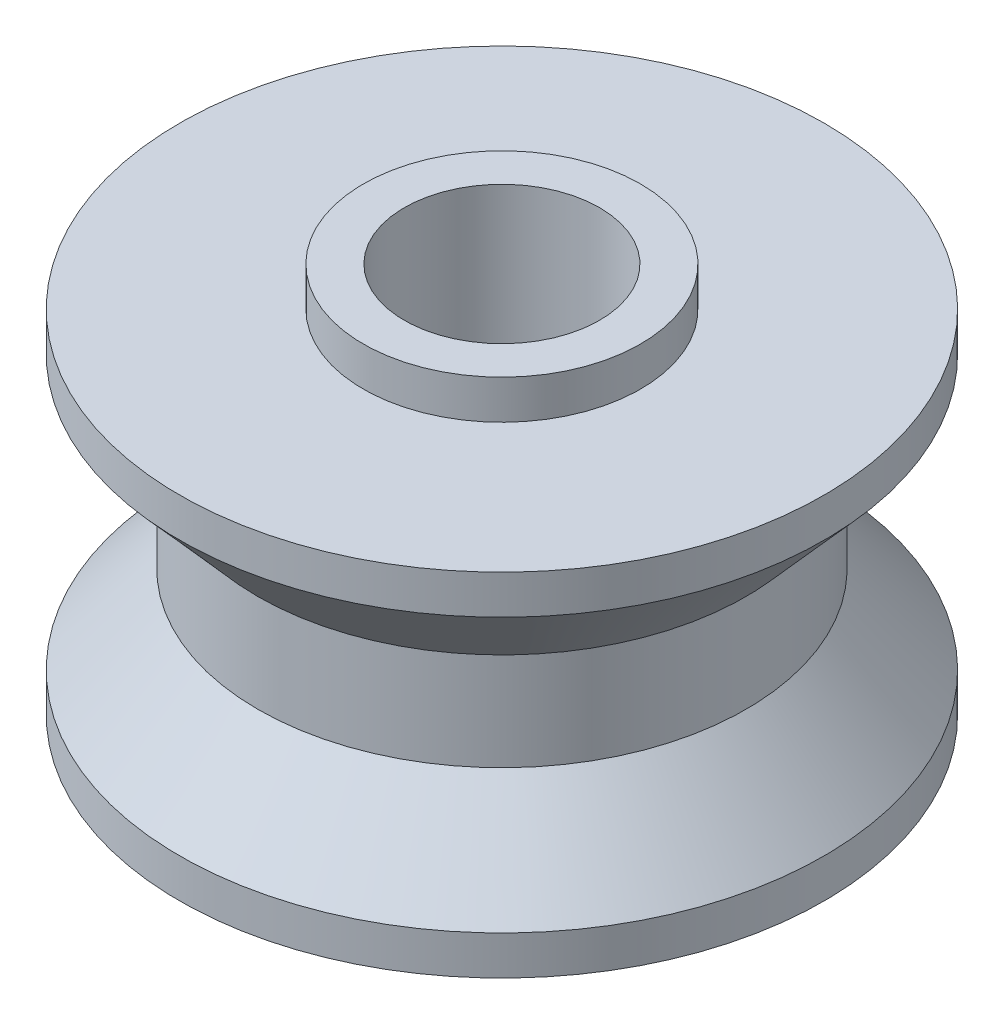
SolidWorks part; units mm, degrees
material "不锈钢 (铁素体)"
ref_plane "前视基准面" through (0, 0, 0) normal (0, 0, 1) x (1, 0, 0)
ref_plane "上视基准面" through (0, 0, 0) normal (0, 1, 0) x (1, 0, 0)
ref_plane "右视基准面" through (0, 0, 0) normal (1, 0, 0) x (0, 0, -1)
sketch "草图1" plane through (0, 0, 0) normal (0, 0, 1) x (1, 0, 0)
  line L0 (2.5, 5.5) -> (3.55, 5.5)
  line L1 (3.55, 5.5) -> (3.55, 4.5)
  line L2 (3.55, 4.5) -> (8.25, 4.5)
  line L3 (8.25, 4.5) -> (8.25, 3.5)
  line L4 (8.25, 3.5) -> (6.25, 1.25)
  line L5 (6.25, 1.25) -> (6.25, -1.25)
  line L6 (0, 0) -> (6.25, 0) construction
  line L7 (2.5, 5.5) -> (2.5, -5.5)
  line L8 (0, 0) -> (0, 4.5455) construction
  line L9 (8.25, -3.5) -> (6.25, -1.25)
  line L10 (8.25, -4.5) -> (8.25, -3.5)
  line L11 (3.55, -4.5) -> (8.25, -4.5)
  line L12 (3.55, -5.5) -> (3.55, -4.5)
  line L13 (2.5, -5.5) -> (3.55, -5.5)
  dimension "D1" = 2.5
  dimension "D2" = 5
  dimension "D3" = 7
  dimension "D4" = 9
  dimension "D5" = 11
  dimension "D6" = 7.1
  dimension "D7" = 12.5
  dimension "D8" = 16.5
revolve "旋转1" add sketch "草图1" angle 360 about L8
